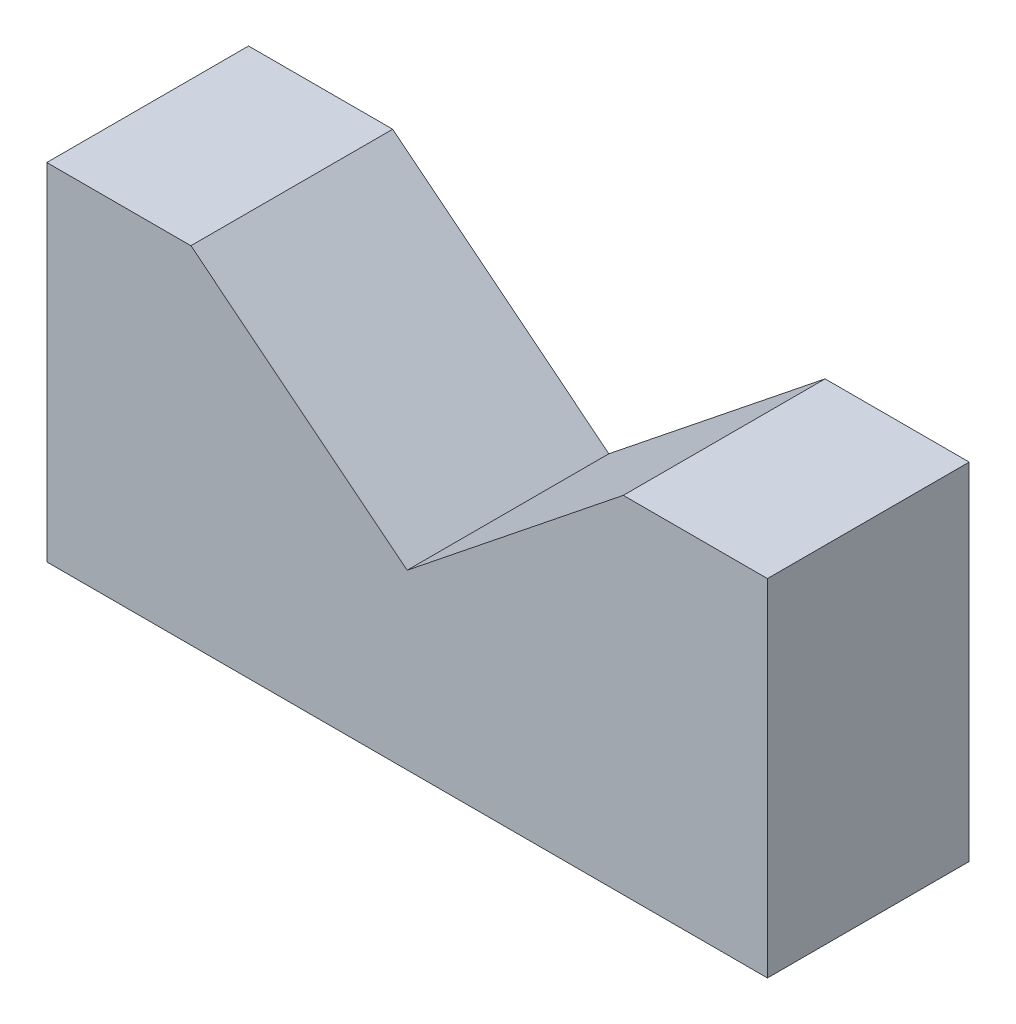
SolidWorks part; units mm, degrees
ref_plane "Ön Düzlem" through (0, 0, 0) normal (0, 0, 1) x (1, 0, 0)
ref_plane "Üst Düzlem" through (0, 0, 0) normal (0, 1, 0) x (1, 0, 0)
ref_plane "Sağ Düzlem" through (0, 0, 0) normal (1, 0, 0) x (0, 0, -1)
sketch "Çizim1" plane through (0, 0, 0) normal (0, 0, 1) x (1, 0, 0)
  line L0 (-125, 0) -> (125, 0)
  line L1 (-125, 0) -> (-125, 120)
  line L2 (125, 0) -> (125, 120)
  line L3 (-125, 120) -> (-75, 120)
  line L4 (125, 120) -> (75, 120)
  line L6 (-75, 120) -> (0, 60)
  line L7 (0, 60) -> (75, 120)
  dimension "D1" = 120
  dimension "D2" = 50
  dimension "D3" = 250
  dimension "D4" = 60
  dimension "D5" = 50
extrude "Yükseklik-Ekstrüzyon1" add sketch "Çizim1" along normal blind 70
